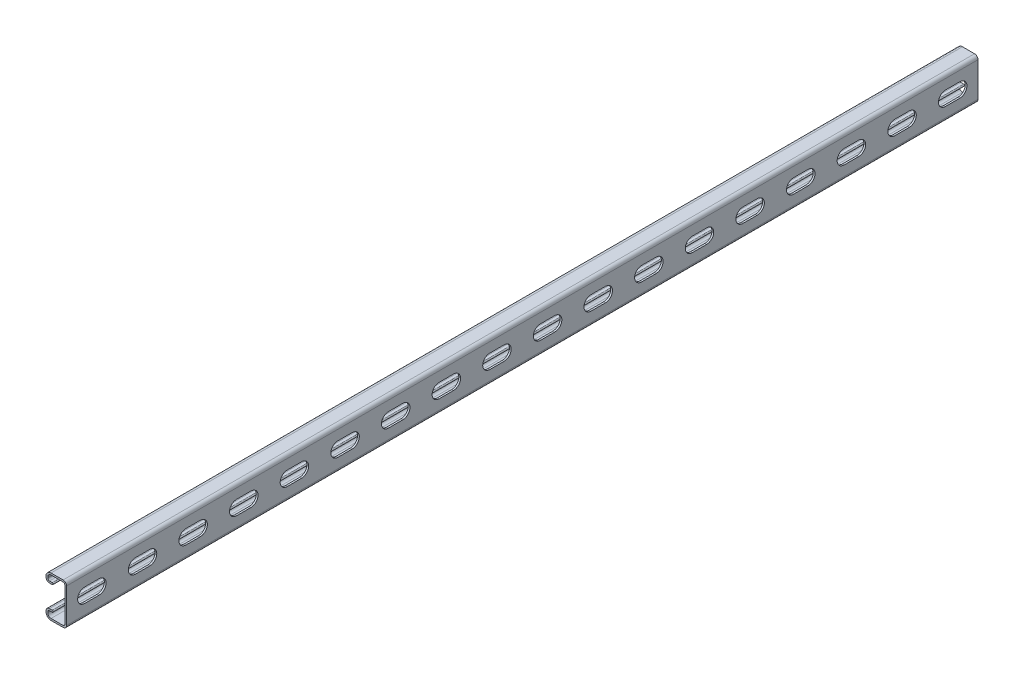
SolidWorks part; units mm, degrees
ref_plane "Front Plane" through (0, 0, 0) normal (0, 0, 1) x (1, 0, 0)
ref_plane "Top Plane" through (0, 0, 0) normal (0, 1, 0) x (1, 0, 0)
ref_plane "Right Plane" through (0, 0, 0) normal (1, 0, 0) x (0, 0, -1)
sketch "Sketch1" plane through (0, 0, 0) normal (0, 0, 1) x (1, 0, 0)
  line L0 (0, 0) -> (-20.6375, 0) construction
  line L3 (-20.6375, 20.6375) -> (0, 20.6375) construction
  line L4 (-20.6375, 20.6375) -> (-20.6375, -20.6375) construction
  line L5 (-20.6375, -20.6375) -> (0, -20.6375) construction
  line L6 (0, 20.6375) -> (0, -20.6375) construction
  line L7 (-15.5892, 20.6375) -> (-3.4607, 20.6375)
  line L8 (0, 17.1767) -> (0, -17.1767)
  line L9 (-1.778, -17.1767) -> (-1.778, 17.1767)
  line L10 (-3.4607, 18.8595) -> (-15.5892, 18.8595)
  line L11 (-20.6375, 15.5892) -> (-20.6375, 14.5732)
  line L12 (-17.1767, 11.1125) -> (-14.3891, 11.1125)
  line L14 (-14.3891, 12.8905) -> (-17.1767, 12.8905)
  line L15 (-18.8595, 14.5732) -> (-18.8595, 15.5892)
  line L16 (-18.8595, -14.5732) -> (-18.8595, -15.5892)
  line L17 (-14.3891, -12.8905) -> (-17.1767, -12.8905)
  line L18 (-17.1767, -11.1125) -> (-14.3891, -11.1125)
  line L19 (-20.6375, -15.5892) -> (-20.6375, -14.5732)
  line L20 (-3.4607, -18.8595) -> (-15.5892, -18.8595)
  line L21 (-15.5892, -20.6375) -> (-3.4607, -20.6375)
  line L22 (-1.778, -20.6375) -> (-1.778, 20.6375) construction
  arc A1 (0, 17.1767) -> (-3.4607, 20.6375) centre (-3.4607, 17.1767) ccw
  arc A2 (-1.778, 17.1767) -> (-3.4607, 18.8595) centre (-3.4607, 17.1767) ccw
  arc A4 (-15.5892, 20.6375) -> (-20.6375, 15.5892) centre (-15.5892, 15.5892) ccw
  arc A5 (-20.6375, 14.5732) -> (-17.1767, 11.1125) centre (-17.1767, 14.5732) ccw
  arc A6 (-14.3891, 11.1125) -> (-14.3891, 12.8905) centre (-14.3891, 12.0015) ccw
  arc A7 (-17.1767, 12.8905) -> (-18.8595, 14.5732) centre (-17.1767, 14.5732) cw
  arc A8 (-18.8595, 15.5892) -> (-15.5892, 18.8595) centre (-15.5892, 15.5892) cw
  arc A9 (-18.8595, -15.5892) -> (-15.5892, -18.8595) centre (-15.5892, -15.5892) ccw
  arc A10 (-17.1767, -12.8905) -> (-18.8595, -14.5732) centre (-17.1767, -14.5732) ccw
  arc A11 (-14.3891, -11.1125) -> (-14.3891, -12.8905) centre (-14.3891, -12.0015) cw
  arc A12 (-20.6375, -14.5732) -> (-17.1767, -11.1125) centre (-17.1767, -14.5732) cw
  arc A13 (-15.5892, -20.6375) -> (-20.6375, -15.5892) centre (-15.5892, -15.5892) cw
  arc A14 (-1.778, -17.1767) -> (-3.4607, -18.8595) centre (-3.4607, -17.1767) cw
  arc A15 (0, -17.1767) -> (-3.4607, -20.6375) centre (-3.4607, -17.1767) cw
  point P24 (0, 20.6375)
  point P65 (-1.778, 0)
  dimension "D1" = 3.4608
  dimension "D2" = 5.0482
  dimension "D3" = 3.4608
  dimension "Ht." = 20.6375
  dimension "Wd." = 41.275
  dimension "Thk." = 1.778
  dimension "D4" = 9.525
  dimension "D5" = 7.1374
extrude "Boss-Extrude1" add sketch "Sketch1" against normal blind 914.4
sketch "Sketch3" plane through (0, 0, 0) normal (1, 0, 0) x (0, 0, -1)
  line L0 (0, 0) -> (914.4, 0) construction
  point P2 (101.6, 0)
  point P3 (812.8, 0)
  dimension "D1" = 101.6
  dimension "D2" = 101.6
  dimension "D3" = 914.4
sketch "Sketch2" plane through (0, 0, 0) normal (1, 0, 0) x (0, 0, -1)
  line L0 (18.2562, 0) -> (32.5437, 0) construction
  line L1 (18.2562, 7.1437) -> (32.5437, 7.1437)
  line L2 (18.2562, -7.1437) -> (32.5437, -7.1437)
  line L3 (18.2562, 0) -> (0, 0) construction
  line L4 (25.4, 0) -> (76.2, 0) construction
  line L5 (0, -17.1767) -> (0, 17.1767) construction
  arc A0 (18.2562, 7.1437) -> (18.2562, -7.1437) centre (18.2562, 0) ccw
  arc A1 (32.5437, -7.1437) -> (32.5437, 7.1437) centre (32.5437, 0) ccw
  point P3 (25.4, 0)
  dimension "Slot Lg." = 28.575
  dimension "D2" = 25.4
  dimension "Slot Wd." = 14.2875
  dimension "Slot Ctr." = 50.8
  dimension "Hole to End" = 11.1125
extrude "Cut-Extrude1" cut sketch "Sketch2" against normal up to vertex (1.778 mm away) up to point (-1.778, 0, 0)
pattern_linear "LPattern1" count 18 spacing 50.8 along (0, 0, 1) of "Cut-Extrude1"
equation "\"D1@LPattern1\" = \"Slot Ctr.@Sketch2\""
equation "\"Hole Count@LPattern1\" = \"Lg.@Boss-Extrude1\" / \"D1@LPattern1\""
equation "\"D3@Sketch3\" = \"Lg.@Boss-Extrude1\""
